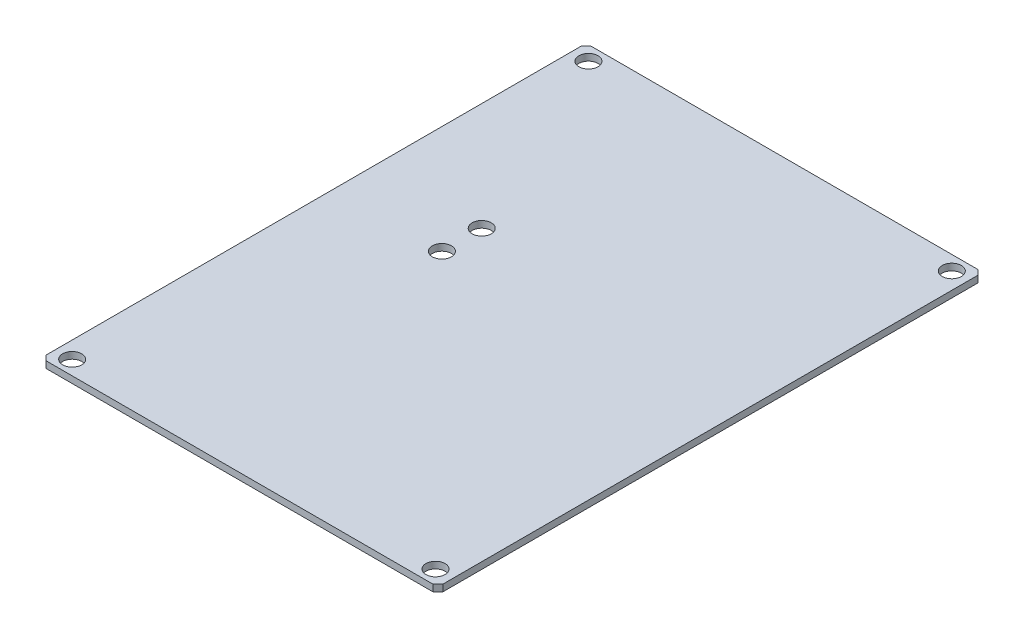
SolidWorks part; units mm, degrees
ref_plane "Front Plane" through (0, 0, 0) normal (0, 0, 1) x (1, 0, 0)
ref_plane "Top Plane" through (0, 0, 0) normal (0, 1, 0) x (1, 0, 0)
ref_plane "Right Plane" through (0, 0, 0) normal (1, 0, 0) x (0, 0, -1)
sketch "Sketch1" plane through (0, 0, 0) normal (0, 1, 0) x (1, 0, 0)
  line L17 (21.25, -27.4901) -> (19.2401, -29.5)
  line L33 (-21.25, 29.5) -> (21.25, 29.5)
  line L34 (-21.25, 29.5) -> (-21.25, -29.5)
  line L35 (-21.25, -29.5) -> (21.25, -29.5)
  line L36 (21.25, 29.5) -> (21.25, -29.5)
  line L37 (-21.25, 29.5) -> (21.25, -29.5) construction
  line L38 (-21.25, -29.5) -> (21.25, 29.5) construction
  line L39 (0, -29.5) -> (0, 29.5) construction
  line L40 (-21.25, -27.4901) -> (-19.2401, -29.5)
  line L41 (21.25, 0) -> (-21.25, 0) construction
  line L42 (21.25, 27.4901) -> (19.2401, 29.5)
  line L43 (-21.25, 27.4901) -> (-19.2401, 29.5)
  line L44 (-20.2401, 28.5) -> (20.2401, 28.5)
  line L45 (-20.2401, -28.5) -> (20.2401, -28.5)
  line L46 (-20.75, -27.9901) -> (-20.75, 27.9901)
  line L47 (20.75, 27.9901) -> (20.75, -27.9901)
  line L48 (-12.1984, 29.75) -> (-12.1984, 25.05) construction
  line L49 (-16.9734, 28.5) -> (-7.4234, 28.5) construction
  line L50 (-16.9734, 28.5) -> (-16.9734, 26.3) construction
  line L51 (-16.9734, 26.3) -> (-7.4234, 26.3) construction
  line L52 (-7.4234, 28.5) -> (-7.4234, 26.3) construction
  line L53 (-16.9734, 28.5) -> (-7.4234, 26.3) construction
  line L54 (-16.9734, 26.3) -> (-7.4234, 28.5) construction
  line L55 (-9.3386, 29.75) -> (-15.0582, 29.75) construction
  point P4 (0, 0)
  point P12 (-16.3873, 25.05)
  point P14 (0, 0)
  point P43 (-12.1984, 27.4)
  point P48 (-12.1984, 27.4)
  dimension "D1" = 42.5
  dimension "D6" = 2.0099
  dimension "D5" = 2.0099
  dimension "D2" = 59
  dimension "D12" = 1
  dimension "D11" = 1
  dimension "D13" = 0.5
  dimension "D14" = 0.5
  dimension "D15" = 9.55
  dimension "D16" = 2.2
extrude "Boss-Extrude1" add sketch "Sketch1" along normal blind 0.7
sketch "Sketch2" plane through (0, 0.7, 0) normal (0, 1, 0) x (1, 0, 0)
  line L1 (-18, -29) -> (18, -29)
  line L2 (-18, -29) -> (-18, -26)
  line L3 (-18, -26) -> (18, -26)
  line L4 (18, -29) -> (18, -26)
  line L5 (-18, -29) -> (18, -26) construction
  line L6 (-18, -26) -> (18, -29) construction
  line L7 (0, 0) -> (0, -29) construction
  line L9 (-20.2401, -28.5) -> (20.2401, -28.5) construction
  point P4 (0, -27.5)
  dimension "D1" = 2.5
  dimension "D2" = 18
  dimension "D3" = 0.5
extrude "Cut-Extrude1" [suppressed] cut sketch "Sketch2" against normal blind 10 contours L3 L4 L1 L2
sketch "Sketch4" plane through (0, 0.7, 0) normal (0, 1, 0) x (1, 0, 0)
  line L0 (-20.2401, 28.5) -> (20.2401, 28.5) construction
  line L1 (15.75, -25.5) -> (-15.75, -25.5)
  line L2 (17.75, -23.5) -> (17.75, 23.5)
  line L3 (15.75, 25.5) -> (-15.75, 25.5)
  line L4 (-17.75, -23.5) -> (-17.75, 23.5)
  line L5 (17.75, -25.5) -> (-17.75, 25.5) construction
  line L6 (17.75, 25.5) -> (-17.75, -25.5) construction
  line L7 (-6, 28.5) -> (6, 28.5)
  line L8 (-6, 28.5) -> (-6, 15.5)
  line L9 (-6, 15.5) -> (6, 15.5)
  line L10 (6, 28.5) -> (6, 15.5)
  line L11 (-6, 28.5) -> (6, 15.5) construction
  line L12 (-6, 15.5) -> (6, 28.5) construction
  line L13 (0, 28.5) -> (0, 17.5887) construction
  line L14 (20.75, 27.9901) -> (20.75, -27.9901) construction
  line L15 (-20.2401, -28.5) -> (20.2401, -28.5) construction
  line L16 (-17.75, 23.5) -> (-15.75, 25.5)
  line L17 (17.75, 23.5) -> (15.75, 25.5)
  line L18 (17.75, -23.5) -> (15.75, -25.5)
  line L19 (-15.75, -25.5) -> (-17.75, -23.5)
  point P0 (0, 0)
  point P10 (0, 22)
  dimension "D1" = 13
  dimension "D2" = 6
  dimension "D3" = 3
  dimension "D4" = 3
extrude "Cut-Extrude2" [suppressed] cut sketch "Sketch4" against normal blind 10 contours L19 L1 L18 L2 L17 L3 L10 L9 L8 L16 L4
fillet "Fillet1" [suppressed] radius 1
sketch "Sketch5" plane through (0, 0.7, 0) normal (0, 1, 0) x (1, 0, 0)
  circle A0 centre (-19, 27) radius 1
  circle A1 centre (19, 27) radius 1
  circle A2 centre (19, -27) radius 1
  circle A3 centre (-19, -27) radius 1
  point P12 (0, 0)
  point P13 (-19, 27)
  point P15 (0, 0)
extrude "Cut-Extrude3" cut sketch "Sketch5" against normal blind 5
sketch "Sketch6" plane through (0, 0.7, 0) normal (0, 1, 0) x (1, 0, 0)
  circle A0 centre (-9.45, 6.2845) radius 1
  circle A1 centre (-9.45, 2.1155) radius 1
extrude "Cut-Extrude4" cut sketch "Sketch6" against normal blind 6
